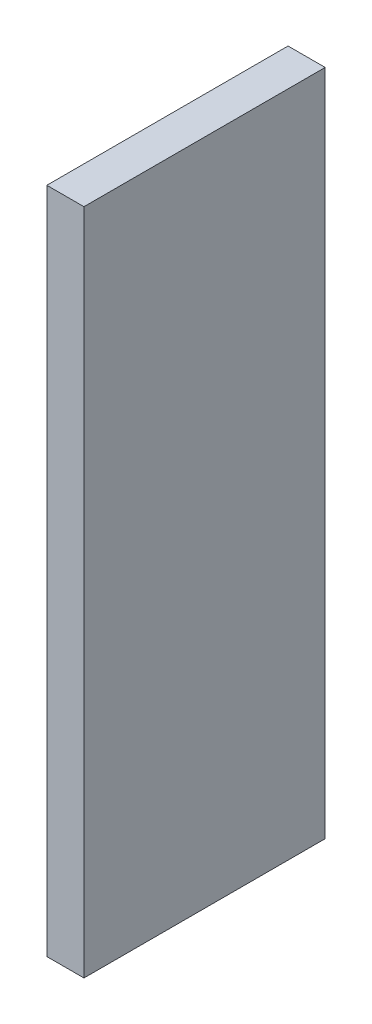
SolidWorks part; units mm, degrees
material "Rubber"
ref_plane "Alzado" through (0, 0, 0) normal (0, 0, 1) x (1, 0, 0)
ref_plane "Planta" through (0, 0, 0) normal (0, 1, 0) x (1, 0, 0)
ref_plane "Vista lateral" through (0, 0, 0) normal (1, 0, 0) x (0, 0, -1)
sketch "Sketch1" plane through (0, 0, 0) normal (0, 0, -1) x (1, 0, 0)
  line L0 (0, -18) -> (2, -18)
  line L1 (0, 0) -> (2, 0) construction
  line L2 (0, 0) -> (0, 18)
  line L3 (0, 18) -> (2, 18)
  line L4 (2, 0) -> (2, 18)
  line L23 (0, -18) -> (0, 0)
  line L24 (2, -18) -> (2, 0)
  dimension "D1" = 2
  dimension "D2" = 36
extrude "Boss-Extrude1" add sketch "Sketch1" along normal blind 13
